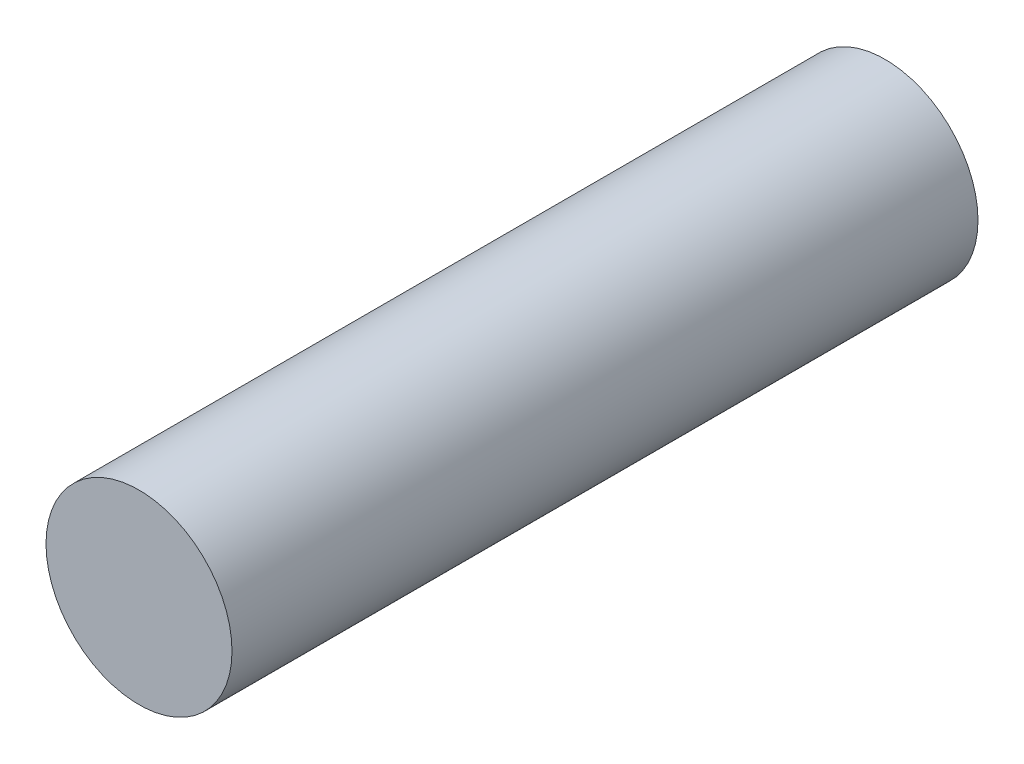
SolidWorks part; units mm, degrees
material "Plain Carbon Steel"
ref_plane "Front Plane" through (0, 0, 0) normal (0, 0, 1) x (1, 0, 0)
ref_plane "Top Plane" through (0, 0, 0) normal (0, 1, 0) x (1, 0, 0)
ref_plane "Right Plane" through (0, 0, 0) normal (1, 0, 0) x (0, 0, -1)
sketch "Sketch1" plane through (0, 0, 0) normal (0, 0, 1) x (1, 0, 0)
  circle A0 centre (0, 0) radius 2.3749
  dimension "D1" = 4.7498
extrude "Boss-Extrude1" add sketch "Sketch1" along normal blind 19.05
